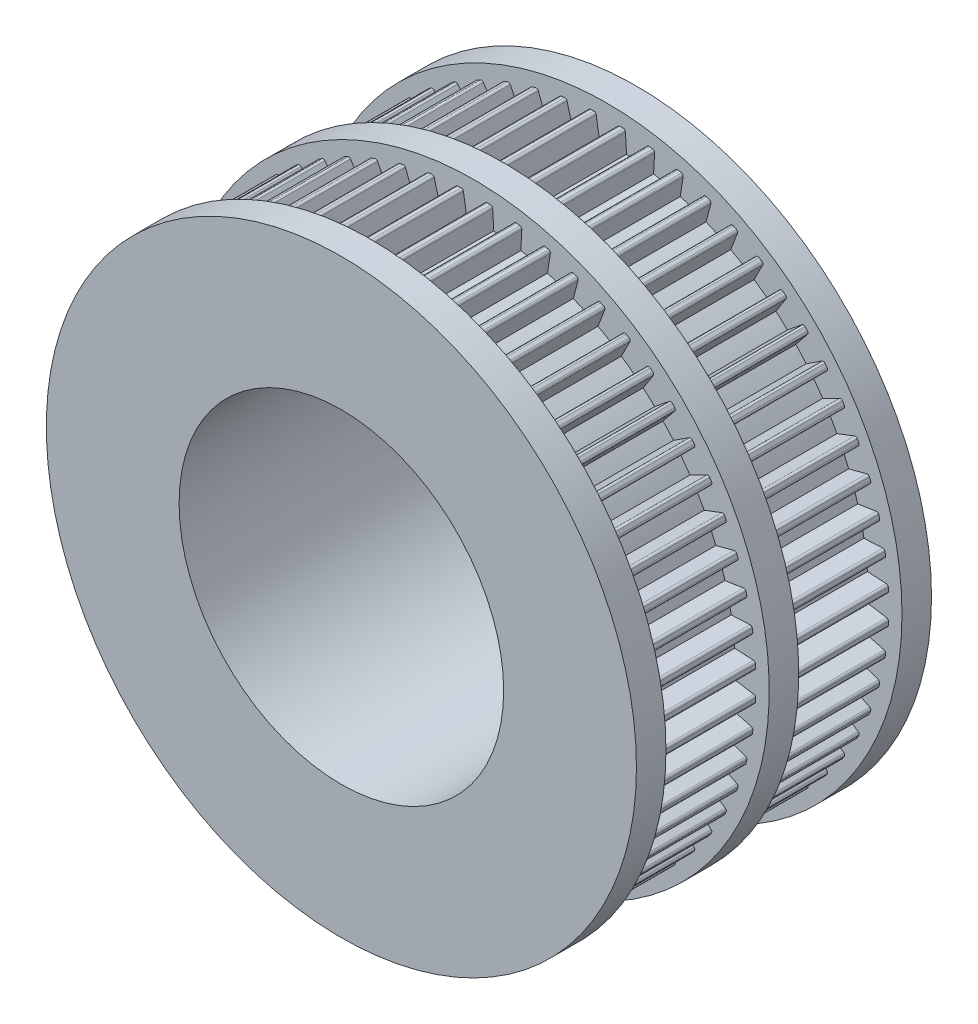
SolidWorks part; units mm, degrees
ref_plane "Front Plane" through (0, 0, 0) normal (0, 0, 1) x (1, 0, 0)
ref_plane "Top Plane" through (0, 0, 0) normal (0, 1, 0) x (1, 0, 0)
ref_plane "Right Plane" through (0, 0, 0) normal (1, 0, 0) x (0, 0, -1)
sketch "Sketch1" plane through (0, 0, 0) normal (0, 0, 1) x (1, 0, 0)
  line L0 (0, 0) -> (0, 9.7797) construction
  line L1 (0, 0) -> (0.9553, 9.0894) construction
  line L2 (-0.7503, 19.0926) -> (-0.527, 17.6995)
  line L3 (1.2496, 19.0664) -> (1.3259, 17.6576) construction
  line L4 (0.7503, 19.0926) -> (0.527, 17.6995)
  line L5 (2.7419, 18.9096) -> (2.3743, 17.5474) construction
  line L6 (1.2496, 19.0664) -> (1.3259, 17.6576)
  line L7 (2.7419, 18.9096) -> (2.3743, 17.5474)
  line L8 (3.2357, 18.8314) -> (3.1644, 17.4223)
  line L9 (4.7034, 18.5194) -> (4.1955, 17.2031)
  line L10 (5.1864, 18.39) -> (4.9682, 16.9961)
  line L11 (6.6135, 17.9263) -> (5.9707, 16.6703)
  line L12 (7.0803, 17.7471) -> (6.7175, 16.3836)
  line L13 (8.451, 17.1368) -> (7.6805, 15.9549)
  line L14 (8.8966, 16.9098) -> (8.3933, 15.5917)
  line L15 (10.196, 16.1595) -> (9.3062, 15.0647)
  line L16 (10.6154, 15.8872) -> (9.9771, 14.629)
  line L17 (11.8293, 15.0052) -> (10.8299, 14.0094)
  line L18 (12.2179, 14.6906) -> (11.4516, 13.5059)
  line L19 (13.333, 13.6865) -> (12.2349, 12.8006)
  line L20 (13.6865, 13.333) -> (12.8006, 12.2349)
  line L21 (14.6906, 12.2179) -> (13.5059, 11.4516)
  line L22 (15.0052, 11.8293) -> (14.0094, 10.8299)
  line L23 (15.8872, 10.6154) -> (14.629, 9.9771)
  line L24 (16.1595, 10.196) -> (15.0647, 9.3062)
  line L25 (16.9098, 8.8966) -> (15.5917, 8.3933)
  line L26 (17.1368, 8.451) -> (15.9549, 7.6805)
  line L27 (17.7471, 7.0803) -> (16.3836, 6.7175)
  line L28 (17.9263, 6.6135) -> (16.6703, 5.9707)
  line L29 (18.39, 5.1864) -> (16.9961, 4.9682)
  line L30 (18.5194, 4.7034) -> (17.2031, 4.1955)
  line L31 (18.8314, 3.2357) -> (17.4223, 3.1644)
  line L32 (18.9096, 2.7419) -> (17.5474, 2.3743)
  line L33 (19.0664, 1.2496) -> (17.6576, 1.3259)
  line L34 (19.0926, 0.7503) -> (17.6995, 0.527)
  line L35 (19.0926, -0.7503) -> (17.6995, -0.527)
  line L36 (19.0664, -1.2496) -> (17.6576, -1.3259)
  line L37 (18.9096, -2.7419) -> (17.5474, -2.3743)
  line L38 (18.8314, -3.2357) -> (17.4223, -3.1644)
  line L39 (18.5194, -4.7034) -> (17.2031, -4.1955)
  line L40 (18.39, -5.1864) -> (16.9961, -4.9682)
  line L41 (17.9263, -6.6135) -> (16.6703, -5.9707)
  line L42 (17.7471, -7.0803) -> (16.3836, -6.7175)
  line L43 (17.1368, -8.451) -> (15.9549, -7.6805)
  line L44 (16.9098, -8.8966) -> (15.5917, -8.3933)
  line L45 (16.1595, -10.196) -> (15.0647, -9.3062)
  line L46 (15.8872, -10.6154) -> (14.629, -9.9771)
  line L47 (15.0052, -11.8293) -> (14.0094, -10.8299)
  line L48 (14.6906, -12.2179) -> (13.5059, -11.4516)
  line L49 (13.6865, -13.333) -> (12.8006, -12.2349)
  line L50 (13.333, -13.6865) -> (12.2349, -12.8006)
  line L51 (12.2179, -14.6906) -> (11.4516, -13.5059)
  line L52 (11.8293, -15.0052) -> (10.8299, -14.0094)
  line L53 (10.6154, -15.8872) -> (9.9771, -14.629)
  line L54 (10.196, -16.1595) -> (9.3062, -15.0647)
  line L55 (8.8966, -16.9098) -> (8.3933, -15.5917)
  line L56 (8.451, -17.1368) -> (7.6805, -15.9549)
  line L57 (7.0803, -17.7471) -> (6.7175, -16.3836)
  line L58 (6.6135, -17.9263) -> (5.9707, -16.6703)
  line L59 (5.1864, -18.39) -> (4.9682, -16.9961)
  line L60 (4.7034, -18.5194) -> (4.1955, -17.2031)
  line L61 (3.2357, -18.8314) -> (3.1644, -17.4223)
  line L62 (2.7419, -18.9096) -> (2.3743, -17.5474)
  line L63 (1.2496, -19.0664) -> (1.3259, -17.6576)
  line L64 (0.7503, -19.0926) -> (0.527, -17.6995)
  line L65 (-0.7503, -19.0926) -> (-0.527, -17.6995)
  line L66 (-1.2496, -19.0664) -> (-1.3259, -17.6576)
  line L67 (-2.7419, -18.9096) -> (-2.3743, -17.5474)
  line L68 (-3.2357, -18.8314) -> (-3.1644, -17.4223)
  line L69 (-4.7034, -18.5194) -> (-4.1955, -17.2031)
  line L70 (-5.1864, -18.39) -> (-4.9682, -16.9961)
  line L71 (-6.6135, -17.9263) -> (-5.9707, -16.6703)
  line L72 (-7.0803, -17.7471) -> (-6.7175, -16.3836)
  line L73 (-8.451, -17.1368) -> (-7.6805, -15.9549)
  line L74 (-8.8966, -16.9098) -> (-8.3933, -15.5917)
  line L75 (-10.196, -16.1595) -> (-9.3062, -15.0647)
  line L76 (-10.6154, -15.8872) -> (-9.9771, -14.629)
  line L77 (-11.8293, -15.0052) -> (-10.8299, -14.0094)
  line L78 (-12.2179, -14.6906) -> (-11.4516, -13.5059)
  line L79 (-13.333, -13.6865) -> (-12.2349, -12.8006)
  line L80 (-13.6865, -13.333) -> (-12.8006, -12.2349)
  line L81 (-14.6906, -12.2179) -> (-13.5059, -11.4516)
  line L82 (-15.0052, -11.8293) -> (-14.0094, -10.8299)
  line L83 (-15.8872, -10.6154) -> (-14.629, -9.9771)
  line L84 (-16.1595, -10.196) -> (-15.0647, -9.3062)
  line L85 (-16.9098, -8.8966) -> (-15.5917, -8.3933)
  line L86 (-17.1368, -8.451) -> (-15.9549, -7.6805)
  line L87 (-17.7471, -7.0803) -> (-16.3836, -6.7175)
  line L88 (-17.9263, -6.6135) -> (-16.6703, -5.9707)
  line L89 (-18.39, -5.1864) -> (-16.9961, -4.9682)
  line L90 (-18.5194, -4.7034) -> (-17.2031, -4.1955)
  line L91 (-18.8314, -3.2357) -> (-17.4223, -3.1644)
  line L92 (-18.9096, -2.7419) -> (-17.5474, -2.3743)
  line L93 (-19.0664, -1.2496) -> (-17.6576, -1.3259)
  line L94 (-19.0926, -0.7503) -> (-17.6995, -0.527)
  line L95 (-19.0926, 0.7503) -> (-17.6995, 0.527)
  line L96 (-19.0664, 1.2496) -> (-17.6576, 1.3259)
  line L97 (-18.9096, 2.7419) -> (-17.5474, 2.3743)
  line L98 (-18.8314, 3.2357) -> (-17.4223, 3.1644)
  line L99 (-18.5194, 4.7034) -> (-17.2031, 4.1955)
  line L100 (-18.39, 5.1864) -> (-16.9961, 4.9682)
  line L101 (-17.9263, 6.6135) -> (-16.6703, 5.9707)
  line L102 (-17.7471, 7.0803) -> (-16.3836, 6.7175)
  line L103 (-17.1368, 8.451) -> (-15.9549, 7.6805)
  line L104 (-16.9098, 8.8966) -> (-15.5917, 8.3933)
  line L105 (-16.1595, 10.196) -> (-15.0647, 9.3062)
  line L106 (-15.8872, 10.6154) -> (-14.629, 9.9771)
  line L107 (-15.0052, 11.8293) -> (-14.0094, 10.8299)
  line L108 (-14.6906, 12.2179) -> (-13.5059, 11.4516)
  line L109 (-13.6865, 13.333) -> (-12.8006, 12.2349)
  line L110 (-13.333, 13.6865) -> (-12.2349, 12.8006)
  line L111 (-12.2179, 14.6906) -> (-11.4516, 13.5059)
  line L112 (-11.8293, 15.0052) -> (-10.8299, 14.0094)
  line L113 (-10.6154, 15.8872) -> (-9.9771, 14.629)
  line L114 (-10.196, 16.1595) -> (-9.3062, 15.0647)
  line L115 (-8.8966, 16.9098) -> (-8.3933, 15.5917)
  line L116 (-8.451, 17.1368) -> (-7.6805, 15.9549)
  line L117 (-7.0803, 17.7471) -> (-6.7175, 16.3836)
  line L118 (-6.6135, 17.9263) -> (-5.9707, 16.6703)
  line L119 (-5.1864, 18.39) -> (-4.9682, 16.9961)
  line L120 (-4.7034, 18.5194) -> (-4.1955, 17.2031)
  line L121 (-3.2357, 18.8314) -> (-3.1644, 17.4223)
  line L122 (-2.7419, 18.9096) -> (-2.3743, 17.5474)
  line L123 (-1.2496, 19.0664) -> (-1.3259, 17.6576)
  arc A0 (2.3743, 17.5474) -> (1.3259, 17.6576) centre (0, 0) ccw construction
  arc A1 (2.7419, 18.9096) -> (1.2496, 19.0664) centre (0, 0) ccw construction
  arc A2 (0.527, 17.6995) -> (-0.527, 17.6995) centre (0, 0) ccw
  arc A3 (0.7503, 19.0926) -> (-0.7503, 19.0926) centre (0, 0) ccw
  arc A4 (2.7419, 18.9096) -> (1.2496, 19.0664) centre (0, 0) ccw
  arc A5 (2.3743, 17.5474) -> (1.3259, 17.6576) centre (0, 0) ccw
  arc A6 (4.7034, 18.5194) -> (3.2357, 18.8314) centre (0, 0) ccw
  arc A7 (4.1955, 17.2031) -> (3.1644, 17.4223) centre (0, 0) ccw
  arc A8 (6.6135, 17.9263) -> (5.1864, 18.39) centre (0, 0) ccw
  arc A9 (5.9707, 16.6703) -> (4.9682, 16.9961) centre (0, 0) ccw
  arc A10 (8.451, 17.1368) -> (7.0803, 17.7471) centre (0, 0) ccw
  arc A11 (7.6805, 15.9549) -> (6.7175, 16.3836) centre (0, 0) ccw
  arc A12 (10.196, 16.1595) -> (8.8966, 16.9098) centre (0, 0) ccw
  arc A13 (9.3062, 15.0647) -> (8.3933, 15.5917) centre (0, 0) ccw
  arc A14 (11.8293, 15.0052) -> (10.6154, 15.8872) centre (0, 0) ccw
  arc A15 (10.8299, 14.0094) -> (9.9771, 14.629) centre (0, 0) ccw
  arc A16 (13.333, 13.6865) -> (12.2179, 14.6906) centre (0, 0) ccw
  arc A17 (12.2349, 12.8006) -> (11.4516, 13.5059) centre (0, 0) ccw
  arc A18 (14.6906, 12.2179) -> (13.6865, 13.333) centre (0, 0) ccw
  arc A19 (13.5059, 11.4516) -> (12.8006, 12.2349) centre (0, 0) ccw
  arc A20 (15.8872, 10.6154) -> (15.0052, 11.8293) centre (0, 0) ccw
  arc A21 (14.629, 9.9771) -> (14.0094, 10.8299) centre (0, 0) ccw
  arc A22 (16.9098, 8.8966) -> (16.1595, 10.196) centre (0, 0) ccw
  arc A23 (15.5917, 8.3933) -> (15.0647, 9.3062) centre (0, 0) ccw
  arc A24 (17.7471, 7.0803) -> (17.1368, 8.451) centre (0, 0) ccw
  arc A25 (16.3836, 6.7175) -> (15.9549, 7.6805) centre (0, 0) ccw
  arc A26 (18.39, 5.1864) -> (17.9263, 6.6135) centre (0, 0) ccw
  arc A27 (16.9961, 4.9682) -> (16.6703, 5.9707) centre (0, 0) ccw
  arc A28 (18.8314, 3.2357) -> (18.5194, 4.7034) centre (0, 0) ccw
  arc A29 (17.4223, 3.1644) -> (17.2031, 4.1955) centre (0, 0) ccw
  arc A30 (19.0664, 1.2496) -> (18.9096, 2.7419) centre (0, 0) ccw
  arc A31 (17.6576, 1.3259) -> (17.5474, 2.3743) centre (0, 0) ccw
  arc A32 (19.0926, -0.7503) -> (19.0926, 0.7503) centre (0, 0) ccw
  arc A33 (17.6995, -0.527) -> (17.6995, 0.527) centre (0, 0) ccw
  arc A34 (18.9096, -2.7419) -> (19.0664, -1.2496) centre (0, 0) ccw
  arc A35 (17.5474, -2.3743) -> (17.6576, -1.3259) centre (0, 0) ccw
  arc A36 (18.5194, -4.7034) -> (18.8314, -3.2357) centre (0, 0) ccw
  arc A37 (17.2031, -4.1955) -> (17.4223, -3.1644) centre (0, 0) ccw
  arc A38 (17.9263, -6.6135) -> (18.39, -5.1864) centre (0, 0) ccw
  arc A39 (16.6703, -5.9707) -> (16.9961, -4.9682) centre (0, 0) ccw
  arc A40 (17.1368, -8.451) -> (17.7471, -7.0803) centre (0, 0) ccw
  arc A41 (15.9549, -7.6805) -> (16.3836, -6.7175) centre (0, 0) ccw
  arc A42 (16.1595, -10.196) -> (16.9098, -8.8966) centre (0, 0) ccw
  arc A43 (15.0647, -9.3062) -> (15.5917, -8.3933) centre (0, 0) ccw
  arc A44 (15.0052, -11.8293) -> (15.8872, -10.6154) centre (0, 0) ccw
  arc A45 (14.0094, -10.8299) -> (14.629, -9.9771) centre (0, 0) ccw
  arc A46 (13.6865, -13.333) -> (14.6906, -12.2179) centre (0, 0) ccw
  arc A47 (12.8006, -12.2349) -> (13.5059, -11.4516) centre (0, 0) ccw
  arc A48 (12.2179, -14.6906) -> (13.333, -13.6865) centre (0, 0) ccw
  arc A49 (11.4516, -13.5059) -> (12.2349, -12.8006) centre (0, 0) ccw
  arc A50 (10.6154, -15.8872) -> (11.8293, -15.0052) centre (0, 0) ccw
  arc A51 (9.9771, -14.629) -> (10.8299, -14.0094) centre (0, 0) ccw
  arc A52 (8.8966, -16.9098) -> (10.196, -16.1595) centre (0, 0) ccw
  arc A53 (8.3933, -15.5917) -> (9.3062, -15.0647) centre (0, 0) ccw
  arc A54 (7.0803, -17.7471) -> (8.451, -17.1368) centre (0, 0) ccw
  arc A55 (6.7175, -16.3836) -> (7.6805, -15.9549) centre (0, 0) ccw
  arc A56 (5.1864, -18.39) -> (6.6135, -17.9263) centre (0, 0) ccw
  arc A57 (4.9682, -16.9961) -> (5.9707, -16.6703) centre (0, 0) ccw
  arc A58 (3.2357, -18.8314) -> (4.7034, -18.5194) centre (0, 0) ccw
  arc A59 (3.1644, -17.4223) -> (4.1955, -17.2031) centre (0, 0) ccw
  arc A60 (1.2496, -19.0664) -> (2.7419, -18.9096) centre (0, 0) ccw
  arc A61 (1.3259, -17.6576) -> (2.3743, -17.5474) centre (0, 0) ccw
  arc A62 (-0.7503, -19.0926) -> (0.7503, -19.0926) centre (0, 0) ccw
  arc A63 (-0.527, -17.6995) -> (0.527, -17.6995) centre (0, 0) ccw
  arc A64 (-2.7419, -18.9096) -> (-1.2496, -19.0664) centre (0, 0) ccw
  arc A65 (-2.3743, -17.5474) -> (-1.3259, -17.6576) centre (0, 0) ccw
  arc A66 (-4.7034, -18.5194) -> (-3.2357, -18.8314) centre (0, 0) ccw
  arc A67 (-4.1955, -17.2031) -> (-3.1644, -17.4223) centre (0, 0) ccw
  arc A68 (-6.6135, -17.9263) -> (-5.1864, -18.39) centre (0, 0) ccw
  arc A69 (-5.9707, -16.6703) -> (-4.9682, -16.9961) centre (0, 0) ccw
  arc A70 (-8.451, -17.1368) -> (-7.0803, -17.7471) centre (0, 0) ccw
  arc A71 (-7.6805, -15.9549) -> (-6.7175, -16.3836) centre (0, 0) ccw
  arc A72 (-10.196, -16.1595) -> (-8.8966, -16.9098) centre (0, 0) ccw
  arc A73 (-9.3062, -15.0647) -> (-8.3933, -15.5917) centre (0, 0) ccw
  arc A74 (-11.8293, -15.0052) -> (-10.6154, -15.8872) centre (0, 0) ccw
  arc A75 (-10.8299, -14.0094) -> (-9.9771, -14.629) centre (0, 0) ccw
  arc A76 (-13.333, -13.6865) -> (-12.2179, -14.6906) centre (0, 0) ccw
  arc A77 (-12.2349, -12.8006) -> (-11.4516, -13.5059) centre (0, 0) ccw
  arc A78 (-14.6906, -12.2179) -> (-13.6865, -13.333) centre (0, 0) ccw
  arc A79 (-13.5059, -11.4516) -> (-12.8006, -12.2349) centre (0, 0) ccw
  arc A80 (-15.8872, -10.6154) -> (-15.0052, -11.8293) centre (0, 0) ccw
  arc A81 (-14.629, -9.9771) -> (-14.0094, -10.8299) centre (0, 0) ccw
  arc A82 (-16.9098, -8.8966) -> (-16.1595, -10.196) centre (0, 0) ccw
  arc A83 (-15.5917, -8.3933) -> (-15.0647, -9.3062) centre (0, 0) ccw
  arc A84 (-17.7471, -7.0803) -> (-17.1368, -8.451) centre (0, 0) ccw
  arc A85 (-16.3836, -6.7175) -> (-15.9549, -7.6805) centre (0, 0) ccw
  arc A86 (-18.39, -5.1864) -> (-17.9263, -6.6135) centre (0, 0) ccw
  arc A87 (-16.9961, -4.9682) -> (-16.6703, -5.9707) centre (0, 0) ccw
  arc A88 (-18.8314, -3.2357) -> (-18.5194, -4.7034) centre (0, 0) ccw
  arc A89 (-17.4223, -3.1644) -> (-17.2031, -4.1955) centre (0, 0) ccw
  arc A90 (-19.0664, -1.2496) -> (-18.9096, -2.7419) centre (0, 0) ccw
  arc A91 (-17.6576, -1.3259) -> (-17.5474, -2.3743) centre (0, 0) ccw
  arc A92 (-19.0926, 0.7503) -> (-19.0926, -0.7503) centre (0, 0) ccw
  arc A93 (-17.6995, 0.527) -> (-17.6995, -0.527) centre (0, 0) ccw
  arc A94 (-18.9096, 2.7419) -> (-19.0664, 1.2496) centre (0, 0) ccw
  arc A95 (-17.5474, 2.3743) -> (-17.6576, 1.3259) centre (0, 0) ccw
  arc A96 (-18.5194, 4.7034) -> (-18.8314, 3.2357) centre (0, 0) ccw
  arc A97 (-17.2031, 4.1955) -> (-17.4223, 3.1644) centre (0, 0) ccw
  arc A98 (-17.9263, 6.6135) -> (-18.39, 5.1864) centre (0, 0) ccw
  arc A99 (-16.6703, 5.9707) -> (-16.9961, 4.9682) centre (0, 0) ccw
  arc A100 (-17.1368, 8.451) -> (-17.7471, 7.0803) centre (0, 0) ccw
  arc A101 (-15.9549, 7.6805) -> (-16.3836, 6.7175) centre (0, 0) ccw
  arc A102 (-16.1595, 10.196) -> (-16.9098, 8.8966) centre (0, 0) ccw
  arc A103 (-15.0647, 9.3062) -> (-15.5917, 8.3933) centre (0, 0) ccw
  arc A104 (-15.0052, 11.8293) -> (-15.8872, 10.6154) centre (0, 0) ccw
  arc A105 (-14.0094, 10.8299) -> (-14.629, 9.9771) centre (0, 0) ccw
  arc A106 (-13.6865, 13.333) -> (-14.6906, 12.2179) centre (0, 0) ccw
  arc A107 (-12.8006, 12.2349) -> (-13.5059, 11.4516) centre (0, 0) ccw
  arc A108 (-12.2179, 14.6906) -> (-13.333, 13.6865) centre (0, 0) ccw
  arc A109 (-11.4516, 13.5059) -> (-12.2349, 12.8006) centre (0, 0) ccw
  arc A110 (-10.6154, 15.8872) -> (-11.8293, 15.0052) centre (0, 0) ccw
  arc A111 (-9.9771, 14.629) -> (-10.8299, 14.0094) centre (0, 0) ccw
  arc A112 (-8.8966, 16.9098) -> (-10.196, 16.1595) centre (0, 0) ccw
  arc A113 (-8.3933, 15.5917) -> (-9.3062, 15.0647) centre (0, 0) ccw
  arc A114 (-7.0803, 17.7471) -> (-8.451, 17.1368) centre (0, 0) ccw
  arc A115 (-6.7175, 16.3836) -> (-7.6805, 15.9549) centre (0, 0) ccw
  arc A116 (-5.1864, 18.39) -> (-6.6135, 17.9263) centre (0, 0) ccw
  arc A117 (-4.9682, 16.9961) -> (-5.9707, 16.6703) centre (0, 0) ccw
  arc A118 (-3.2357, 18.8314) -> (-4.7034, 18.5194) centre (0, 0) ccw
  arc A119 (-3.1644, 17.4223) -> (-4.1955, 17.2031) centre (0, 0) ccw
  arc A120 (-1.2496, 19.0664) -> (-2.7419, 18.9096) centre (0, 0) ccw
  arc A121 (-1.3259, 17.6576) -> (-2.3743, 17.5474) centre (0, 0) ccw
  point P1 (0, 19.1073)
  point P2 (1.9973, 19.0027)
  point P253 (0, 0)
  dimension "D1" = 1.4
  dimension "D2" = 0.8
  dimension "D3" = 0.5
  dimension "D4" = 2
  dimension "D5" = 60
sketch "Sketch2" plane through (0, 0, 0) normal (0, 0, 1) x (1, 0, 0)
  circle A0 centre (0, 0) radius 19.1073
extrude "Boss-Extrude1" add sketch "Sketch2" along normal blind 7
extrude "Cut-Extrude1" cut sketch "Sketch1" along normal blind 22
fillet "Fillet1" radius 0.15 4 edges at (-8.3933, 15.5917, 3.5) (-8.8966, 16.9098, 3.5) (-7.6805, 15.9549, 3.5) (-8.451, 17.1368, 3.5)
sketch "Sketch3" plane through (0, 0, 0) normal (0, 0, -1) x (-1, 0, 0)
  circle A0 centre (0, 0) radius 8
  dimension "D1" = 16
extrude "Cut-Extrude2" cut sketch "Sketch3" against normal blind 22
sketch "Sketch5" plane through (0, 0, 7) normal (0, 0, 1) x (1, 0, 0)
  line L0 (-0.527, 17.6995) -> (-0.7503, 19.0926) construction
  line L1 (-1.2496, 19.0664) -> (-1.3259, 17.6576) construction
  line L2 (0.7503, 19.0926) -> (0.7291, 18.9607)
  line L3 (1.2568, 18.9331) -> (1.2496, 19.0664)
  line L4 (-0.7291, 18.9607) -> (-0.7503, 19.0926)
  line L5 (-1.2496, 19.0664) -> (-1.2568, 18.9331)
  line L6 (2.7419, 18.9096) -> (2.7071, 18.7807)
  line L7 (3.229, 18.698) -> (3.2357, 18.8314)
  line L8 (4.7034, 18.5194) -> (4.6554, 18.3948)
  line L9 (5.1657, 18.2581) -> (5.1864, 18.39)
  line L10 (6.6135, 17.9263) -> (6.5526, 17.8074)
  line L11 (7.0459, 17.6181) -> (7.0803, 17.7471)
  line L12 (8.451, 17.1368) -> (8.3781, 17.0249)
  line L13 (8.8489, 16.7851) -> (8.8966, 16.9098)
  line L14 (10.196, 16.1595) -> (10.1118, 16.0559)
  line L15 (10.555, 15.7681) -> (10.6154, 15.8872)
  line L16 (11.8293, 15.0052) -> (11.7347, 14.911)
  line L17 (12.1454, 14.5785) -> (12.2179, 14.6906)
  line L18 (13.333, 13.6865) -> (13.2291, 13.6027)
  line L19 (13.6027, 13.2291) -> (13.6865, 13.333)
  line L20 (14.6906, 12.2179) -> (14.5785, 12.1454)
  line L21 (14.911, 11.7347) -> (15.0052, 11.8293)
  line L22 (15.8872, 10.6154) -> (15.7681, 10.555)
  line L23 (16.0559, 10.1118) -> (16.1595, 10.196)
  line L24 (16.9098, 8.8966) -> (16.7851, 8.8489)
  line L25 (17.0249, 8.3781) -> (17.1368, 8.451)
  line L26 (17.7471, 7.0803) -> (17.6181, 7.0459)
  line L27 (17.8074, 6.5526) -> (17.9263, 6.6135)
  line L28 (18.39, 5.1864) -> (18.2581, 5.1657)
  line L29 (18.3948, 4.6554) -> (18.5194, 4.7034)
  line L30 (18.8314, 3.2357) -> (18.698, 3.229)
  line L31 (18.7807, 2.7071) -> (18.9096, 2.7419)
  line L32 (19.0664, 1.2496) -> (18.9331, 1.2568)
  line L33 (18.9607, 0.7291) -> (19.0926, 0.7503)
  line L34 (19.0926, -0.7503) -> (18.9607, -0.7291)
  line L35 (18.9331, -1.2568) -> (19.0664, -1.2496)
  line L36 (18.9096, -2.7419) -> (18.7807, -2.7071)
  line L37 (18.698, -3.229) -> (18.8314, -3.2357)
  line L38 (18.5194, -4.7034) -> (18.3948, -4.6554)
  line L39 (18.2581, -5.1657) -> (18.39, -5.1864)
  line L40 (17.9263, -6.6135) -> (17.8074, -6.5526)
  line L41 (17.6181, -7.0459) -> (17.7471, -7.0803)
  line L42 (17.1368, -8.451) -> (17.0249, -8.3781)
  line L43 (16.7851, -8.8489) -> (16.9098, -8.8966)
  line L44 (16.1595, -10.196) -> (16.0559, -10.1118)
  line L45 (15.7681, -10.555) -> (15.8872, -10.6154)
  line L46 (15.0052, -11.8293) -> (14.911, -11.7347)
  line L47 (14.5785, -12.1454) -> (14.6906, -12.2179)
  line L48 (13.6865, -13.333) -> (13.6027, -13.2291)
  line L49 (13.2291, -13.6027) -> (13.333, -13.6865)
  line L50 (12.2179, -14.6906) -> (12.1454, -14.5785)
  line L51 (11.7347, -14.911) -> (11.8293, -15.0052)
  line L52 (10.6154, -15.8872) -> (10.555, -15.7681)
  line L53 (10.1118, -16.0559) -> (10.196, -16.1595)
  line L54 (8.8966, -16.9098) -> (8.8489, -16.7851)
  line L55 (8.3781, -17.0249) -> (8.451, -17.1368)
  line L56 (7.0803, -17.7471) -> (7.0459, -17.6181)
  line L57 (6.5526, -17.8074) -> (6.6135, -17.9263)
  line L58 (5.1864, -18.39) -> (5.1657, -18.2581)
  line L59 (4.6554, -18.3948) -> (4.7034, -18.5194)
  line L60 (3.2357, -18.8314) -> (3.229, -18.698)
  line L61 (2.7071, -18.7807) -> (2.7419, -18.9096)
  line L62 (1.2496, -19.0664) -> (1.2568, -18.9331)
  line L63 (0.7291, -18.9607) -> (0.7503, -19.0926)
  line L64 (-0.7503, -19.0926) -> (-0.7291, -18.9607)
  line L65 (-1.2568, -18.9331) -> (-1.2496, -19.0664)
  line L66 (-2.7419, -18.9096) -> (-2.7071, -18.7807)
  line L67 (-3.229, -18.698) -> (-3.2357, -18.8314)
  line L68 (-4.7034, -18.5194) -> (-4.6554, -18.3948)
  line L69 (-5.1657, -18.2581) -> (-5.1864, -18.39)
  line L70 (-6.6135, -17.9263) -> (-6.5526, -17.8074)
  line L71 (-7.0459, -17.6181) -> (-7.0803, -17.7471)
  line L72 (-8.451, -17.1368) -> (-8.3781, -17.0249)
  line L73 (-8.8489, -16.7851) -> (-8.8966, -16.9098)
  line L74 (-10.196, -16.1595) -> (-10.1118, -16.0559)
  line L75 (-10.555, -15.7681) -> (-10.6154, -15.8872)
  line L76 (-11.8293, -15.0052) -> (-11.7347, -14.911)
  line L77 (-12.1454, -14.5785) -> (-12.2179, -14.6906)
  line L78 (-13.333, -13.6865) -> (-13.2291, -13.6027)
  line L79 (-13.6027, -13.2291) -> (-13.6865, -13.333)
  line L80 (-14.6906, -12.2179) -> (-14.5785, -12.1454)
  line L81 (-14.911, -11.7347) -> (-15.0052, -11.8293)
  line L82 (-15.8872, -10.6154) -> (-15.7681, -10.555)
  line L83 (-16.0559, -10.1118) -> (-16.1595, -10.196)
  line L84 (-16.9098, -8.8966) -> (-16.7851, -8.8489)
  line L85 (-17.0249, -8.3781) -> (-17.1368, -8.451)
  line L86 (-17.7471, -7.0803) -> (-17.6181, -7.0459)
  line L87 (-17.8074, -6.5526) -> (-17.9263, -6.6135)
  line L88 (-18.39, -5.1864) -> (-18.2581, -5.1657)
  line L89 (-18.3948, -4.6554) -> (-18.5194, -4.7034)
  line L90 (-18.8314, -3.2357) -> (-18.698, -3.229)
  line L91 (-18.7807, -2.7071) -> (-18.9096, -2.7419)
  line L92 (-19.0664, -1.2496) -> (-18.9331, -1.2568)
  line L93 (-18.9607, -0.7291) -> (-19.0926, -0.7503)
  line L94 (-19.0926, 0.7503) -> (-18.9607, 0.7291)
  line L95 (-18.9331, 1.2568) -> (-19.0664, 1.2496)
  line L96 (-18.9096, 2.7419) -> (-18.7807, 2.7071)
  line L97 (-18.698, 3.229) -> (-18.8314, 3.2357)
  line L98 (-18.5194, 4.7034) -> (-18.3948, 4.6554)
  line L99 (-18.2581, 5.1657) -> (-18.39, 5.1864)
  line L100 (-17.9263, 6.6135) -> (-17.8074, 6.5526)
  line L101 (-17.6181, 7.0459) -> (-17.7471, 7.0803)
  line L102 (-17.1368, 8.451) -> (-17.0249, 8.3781)
  line L103 (-16.7851, 8.8489) -> (-16.9098, 8.8966)
  line L104 (-16.1595, 10.196) -> (-16.0559, 10.1118)
  line L105 (-15.7681, 10.555) -> (-15.8872, 10.6154)
  line L106 (-15.0052, 11.8293) -> (-14.911, 11.7347)
  line L107 (-14.5785, 12.1454) -> (-14.6906, 12.2179)
  line L108 (-13.6865, 13.333) -> (-13.6027, 13.2291)
  line L109 (-13.2291, 13.6027) -> (-13.333, 13.6865)
  line L110 (-12.2179, 14.6906) -> (-12.1454, 14.5785)
  line L111 (-11.7347, 14.911) -> (-11.8293, 15.0052)
  line L112 (-10.6154, 15.8872) -> (-10.555, 15.7681)
  line L113 (-10.1118, 16.0559) -> (-10.196, 16.1595)
  line L114 (-8.8966, 16.9098) -> (-8.8489, 16.7851)
  line L115 (-8.3781, 17.0249) -> (-8.451, 17.1368)
  line L116 (-7.0803, 17.7471) -> (-7.0459, 17.6181)
  line L117 (-6.5526, 17.8074) -> (-6.6135, 17.9263)
  line L118 (-5.1864, 18.39) -> (-5.1657, 18.2581)
  line L119 (-4.6554, 18.3948) -> (-4.7034, 18.5194)
  line L120 (-3.2357, 18.8314) -> (-3.229, 18.698)
  line L121 (-2.7071, 18.7807) -> (-2.7419, 18.9096)
  arc A0 (-0.7503, 19.0926) -> (-1.2496, 19.0664) centre (0, 0) ccw construction
  arc A2 (-0.8842, 19.0869) -> (-0.7291, 18.9607) centre (-0.8772, 18.937) cw
  arc A3 (-1.1158, 19.0747) -> (-1.2568, 18.9331) centre (-1.107, 18.925) ccw
  arc A4 (-0.7503, 19.0926) -> (-0.8842, 19.0869) centre (0, 0) ccw
  arc A5 (-1.1158, 19.0747) -> (-1.2496, 19.0664) centre (0, 0) ccw
  arc A6 (0.8842, 19.0869) -> (0.7291, 18.9607) centre (0.8772, 18.937) ccw
  arc A7 (0.8842, 19.0869) -> (0.7503, 19.0926) centre (0, 0) ccw
  arc A8 (1.1158, 19.0747) -> (1.2568, 18.9331) centre (1.107, 18.925) cw
  arc A9 (1.2496, 19.0664) -> (1.1158, 19.0747) centre (0, 0) ccw
  arc A10 (2.8745, 18.8899) -> (2.7071, 18.7807) centre (2.8519, 18.7416) ccw
  arc A11 (2.8745, 18.8899) -> (2.7419, 18.9096) centre (0, 0) ccw
  arc A12 (3.1035, 18.8536) -> (3.229, 18.698) centre (3.0792, 18.7056) cw
  arc A13 (3.2357, 18.8314) -> (3.1035, 18.8536) centre (0, 0) ccw
  arc A14 (4.8332, 18.4859) -> (4.6554, 18.3948) centre (4.7953, 18.3408) ccw
  arc A15 (4.8332, 18.4859) -> (4.7034, 18.5194) centre (0, 0) ccw
  arc A16 (5.0573, 18.4259) -> (5.1657, 18.2581) centre (5.0176, 18.2813) cw
  arc A17 (5.1864, 18.39) -> (5.0573, 18.4259) centre (0, 0) ccw
  arc A18 (6.7391, 17.8794) -> (6.5526, 17.8074) centre (6.6862, 17.7391) ccw
  arc A19 (6.7391, 17.8794) -> (6.6135, 17.9263) centre (0, 0) ccw
  arc A20 (6.9556, 17.7963) -> (7.0459, 17.6181) centre (6.901, 17.6566) cw
  arc A21 (7.0803, 17.7471) -> (6.9556, 17.7963) centre (0, 0) ccw
  arc A22 (8.5711, 17.0771) -> (8.3781, 17.0249) centre (8.5038, 16.943) ccw
  arc A23 (8.5711, 17.0771) -> (8.451, 17.1368) centre (0, 0) ccw
  arc A24 (8.7777, 16.9718) -> (8.8489, 16.7851) centre (8.7088, 16.8386) cw
  arc A25 (8.8966, 16.9098) -> (8.7777, 16.9718) centre (0, 0) ccw
  arc A26 (10.3092, 16.0876) -> (10.1118, 16.0559) centre (10.2282, 15.9613) ccw
  arc A27 (10.3092, 16.0876) -> (10.196, 16.1595) centre (0, 0) ccw
  arc A28 (10.5037, 15.9613) -> (10.555, 15.7681) centre (10.4212, 15.836) cw
  arc A29 (10.6154, 15.8872) -> (10.5037, 15.9613) centre (0, 0) ccw
  arc A30 (11.9343, 14.9219) -> (11.7347, 14.911) centre (11.8406, 14.8047) ccw
  arc A31 (11.9343, 14.9219) -> (11.8293, 15.0052) centre (0, 0) ccw
  arc A32 (12.1145, 14.7759) -> (12.1454, 14.5785) centre (12.0194, 14.6599) cw
  arc A33 (12.2179, 14.6906) -> (12.1145, 14.7759) centre (0, 0) ccw
  arc A34 (13.4287, 13.5927) -> (13.2291, 13.6027) centre (13.3233, 13.486) ccw
  arc A35 (13.4287, 13.5927) -> (13.333, 13.6865) centre (0, 0) ccw
  arc A36 (13.5927, 13.4287) -> (13.6027, 13.2291) centre (13.486, 13.3233) cw
  arc A37 (13.6865, 13.333) -> (13.5927, 13.4287) centre (0, 0) ccw
  arc A38 (14.7759, 12.1145) -> (14.5785, 12.1454) centre (14.6599, 12.0194) ccw
  arc A39 (14.7759, 12.1145) -> (14.6906, 12.2179) centre (0, 0) ccw
  arc A40 (14.9219, 11.9343) -> (14.911, 11.7347) centre (14.8047, 11.8406) cw
  arc A41 (15.0052, 11.8293) -> (14.9219, 11.9343) centre (0, 0) ccw
  arc A42 (15.9613, 10.5037) -> (15.7681, 10.555) centre (15.836, 10.4212) ccw
  arc A43 (15.9613, 10.5037) -> (15.8872, 10.6154) centre (0, 0) ccw
  arc A44 (16.0876, 10.3092) -> (16.0559, 10.1118) centre (15.9613, 10.2282) cw
  arc A45 (16.1595, 10.196) -> (16.0876, 10.3092) centre (0, 0) ccw
  arc A46 (16.9718, 8.7777) -> (16.7851, 8.8489) centre (16.8386, 8.7088) ccw
  arc A47 (16.9718, 8.7777) -> (16.9098, 8.8966) centre (0, 0) ccw
  arc A48 (17.0771, 8.5711) -> (17.0249, 8.3781) centre (16.943, 8.5038) cw
  arc A49 (17.1368, 8.451) -> (17.0771, 8.5711) centre (0, 0) ccw
  arc A50 (17.7963, 6.9556) -> (17.6181, 7.0459) centre (17.6566, 6.901) ccw
  arc A51 (17.7963, 6.9556) -> (17.7471, 7.0803) centre (0, 0) ccw
  arc A52 (17.8794, 6.7391) -> (17.8074, 6.5526) centre (17.7391, 6.6862) cw
  arc A53 (17.9263, 6.6135) -> (17.8794, 6.7391) centre (0, 0) ccw
  arc A54 (18.4259, 5.0573) -> (18.2581, 5.1657) centre (18.2813, 5.0176) ccw
  arc A55 (18.4259, 5.0573) -> (18.39, 5.1864) centre (0, 0) ccw
  arc A56 (18.4859, 4.8332) -> (18.3948, 4.6554) centre (18.3408, 4.7953) cw
  arc A57 (18.5194, 4.7034) -> (18.4859, 4.8332) centre (0, 0) ccw
  arc A58 (18.8536, 3.1035) -> (18.698, 3.229) centre (18.7056, 3.0792) ccw
  arc A59 (18.8536, 3.1035) -> (18.8314, 3.2357) centre (0, 0) ccw
  arc A60 (18.8899, 2.8745) -> (18.7807, 2.7071) centre (18.7416, 2.8519) cw
  arc A61 (18.9096, 2.7419) -> (18.8899, 2.8745) centre (0, 0) ccw
  arc A62 (19.0747, 1.1158) -> (18.9331, 1.2568) centre (18.925, 1.107) ccw
  arc A63 (19.0747, 1.1158) -> (19.0664, 1.2496) centre (0, 0) ccw
  arc A64 (19.0869, 0.8842) -> (18.9607, 0.7291) centre (18.937, 0.8772) cw
  arc A65 (19.0926, 0.7503) -> (19.0869, 0.8842) centre (0, 0) ccw
  arc A66 (19.0869, -0.8842) -> (18.9607, -0.7291) centre (18.937, -0.8772) ccw
  arc A67 (19.0869, -0.8842) -> (19.0926, -0.7503) centre (0, 0) ccw
  arc A68 (19.0747, -1.1158) -> (18.9331, -1.2568) centre (18.925, -1.107) cw
  arc A69 (19.0664, -1.2496) -> (19.0747, -1.1158) centre (0, 0) ccw
  arc A70 (18.8899, -2.8745) -> (18.7807, -2.7071) centre (18.7416, -2.8519) ccw
  arc A71 (18.8899, -2.8745) -> (18.9096, -2.7419) centre (0, 0) ccw
  arc A72 (18.8536, -3.1035) -> (18.698, -3.229) centre (18.7056, -3.0792) cw
  arc A73 (18.8314, -3.2357) -> (18.8536, -3.1035) centre (0, 0) ccw
  arc A74 (18.4859, -4.8332) -> (18.3948, -4.6554) centre (18.3408, -4.7953) ccw
  arc A75 (18.4859, -4.8332) -> (18.5194, -4.7034) centre (0, 0) ccw
  arc A76 (18.4259, -5.0573) -> (18.2581, -5.1657) centre (18.2813, -5.0176) cw
  arc A77 (18.39, -5.1864) -> (18.4259, -5.0573) centre (0, 0) ccw
  arc A78 (17.8794, -6.7391) -> (17.8074, -6.5526) centre (17.7391, -6.6862) ccw
  arc A79 (17.8794, -6.7391) -> (17.9263, -6.6135) centre (0, 0) ccw
  arc A80 (17.7963, -6.9556) -> (17.6181, -7.0459) centre (17.6566, -6.901) cw
  arc A81 (17.7471, -7.0803) -> (17.7963, -6.9556) centre (0, 0) ccw
  arc A82 (17.0771, -8.5711) -> (17.0249, -8.3781) centre (16.943, -8.5038) ccw
  arc A83 (17.0771, -8.5711) -> (17.1368, -8.451) centre (0, 0) ccw
  arc A84 (16.9718, -8.7777) -> (16.7851, -8.8489) centre (16.8386, -8.7088) cw
  arc A85 (16.9098, -8.8966) -> (16.9718, -8.7777) centre (0, 0) ccw
  arc A86 (16.0876, -10.3092) -> (16.0559, -10.1118) centre (15.9613, -10.2282) ccw
  arc A87 (16.0876, -10.3092) -> (16.1595, -10.196) centre (0, 0) ccw
  arc A88 (15.9613, -10.5037) -> (15.7681, -10.555) centre (15.836, -10.4212) cw
  arc A89 (15.8872, -10.6154) -> (15.9613, -10.5037) centre (0, 0) ccw
  arc A90 (14.9219, -11.9343) -> (14.911, -11.7347) centre (14.8047, -11.8406) ccw
  arc A91 (14.9219, -11.9343) -> (15.0052, -11.8293) centre (0, 0) ccw
  arc A92 (14.7759, -12.1145) -> (14.5785, -12.1454) centre (14.6599, -12.0194) cw
  arc A93 (14.6906, -12.2179) -> (14.7759, -12.1145) centre (0, 0) ccw
  arc A94 (13.5927, -13.4287) -> (13.6027, -13.2291) centre (13.486, -13.3233) ccw
  arc A95 (13.5927, -13.4287) -> (13.6865, -13.333) centre (0, 0) ccw
  arc A96 (13.4287, -13.5927) -> (13.2291, -13.6027) centre (13.3233, -13.486) cw
  arc A97 (13.333, -13.6865) -> (13.4287, -13.5927) centre (0, 0) ccw
  arc A98 (12.1145, -14.7759) -> (12.1454, -14.5785) centre (12.0194, -14.6599) ccw
  arc A99 (12.1145, -14.7759) -> (12.2179, -14.6906) centre (0, 0) ccw
  arc A100 (11.9343, -14.9219) -> (11.7347, -14.911) centre (11.8406, -14.8047) cw
  arc A101 (11.8293, -15.0052) -> (11.9343, -14.9219) centre (0, 0) ccw
  arc A102 (10.5037, -15.9613) -> (10.555, -15.7681) centre (10.4212, -15.836) ccw
  arc A103 (10.5037, -15.9613) -> (10.6154, -15.8872) centre (0, 0) ccw
  arc A104 (10.3092, -16.0876) -> (10.1118, -16.0559) centre (10.2282, -15.9613) cw
  arc A105 (10.196, -16.1595) -> (10.3092, -16.0876) centre (0, 0) ccw
  arc A106 (8.7777, -16.9718) -> (8.8489, -16.7851) centre (8.7088, -16.8386) ccw
  arc A107 (8.7777, -16.9718) -> (8.8966, -16.9098) centre (0, 0) ccw
  arc A108 (8.5711, -17.0771) -> (8.3781, -17.0249) centre (8.5038, -16.943) cw
  arc A109 (8.451, -17.1368) -> (8.5711, -17.0771) centre (0, 0) ccw
  arc A110 (6.9556, -17.7963) -> (7.0459, -17.6181) centre (6.901, -17.6566) ccw
  arc A111 (6.9556, -17.7963) -> (7.0803, -17.7471) centre (0, 0) ccw
  arc A112 (6.7391, -17.8794) -> (6.5526, -17.8074) centre (6.6862, -17.7391) cw
  arc A113 (6.6135, -17.9263) -> (6.7391, -17.8794) centre (0, 0) ccw
  arc A114 (5.0573, -18.4259) -> (5.1657, -18.2581) centre (5.0176, -18.2813) ccw
  arc A115 (5.0573, -18.4259) -> (5.1864, -18.39) centre (0, 0) ccw
  arc A116 (4.8332, -18.4859) -> (4.6554, -18.3948) centre (4.7953, -18.3408) cw
  arc A117 (4.7034, -18.5194) -> (4.8332, -18.4859) centre (0, 0) ccw
  arc A118 (3.1035, -18.8536) -> (3.229, -18.698) centre (3.0792, -18.7056) ccw
  arc A119 (3.1035, -18.8536) -> (3.2357, -18.8314) centre (0, 0) ccw
  arc A120 (2.8745, -18.8899) -> (2.7071, -18.7807) centre (2.8519, -18.7416) cw
  arc A121 (2.7419, -18.9096) -> (2.8745, -18.8899) centre (0, 0) ccw
  arc A122 (1.1158, -19.0747) -> (1.2568, -18.9331) centre (1.107, -18.925) ccw
  arc A123 (1.1158, -19.0747) -> (1.2496, -19.0664) centre (0, 0) ccw
  arc A124 (0.8842, -19.0869) -> (0.7291, -18.9607) centre (0.8772, -18.937) cw
  arc A125 (0.7503, -19.0926) -> (0.8842, -19.0869) centre (0, 0) ccw
  arc A126 (-0.8842, -19.0869) -> (-0.7291, -18.9607) centre (-0.8772, -18.937) ccw
  arc A127 (-0.8842, -19.0869) -> (-0.7503, -19.0926) centre (0, 0) ccw
  arc A128 (-1.1158, -19.0747) -> (-1.2568, -18.9331) centre (-1.107, -18.925) cw
  arc A129 (-1.2496, -19.0664) -> (-1.1158, -19.0747) centre (0, 0) ccw
  arc A130 (-2.8745, -18.8899) -> (-2.7071, -18.7807) centre (-2.8519, -18.7416) ccw
  arc A131 (-2.8745, -18.8899) -> (-2.7419, -18.9096) centre (0, 0) ccw
  arc A132 (-3.1035, -18.8536) -> (-3.229, -18.698) centre (-3.0792, -18.7056) cw
  arc A133 (-3.2357, -18.8314) -> (-3.1035, -18.8536) centre (0, 0) ccw
  arc A134 (-4.8332, -18.4859) -> (-4.6554, -18.3948) centre (-4.7953, -18.3408) ccw
  arc A135 (-4.8332, -18.4859) -> (-4.7034, -18.5194) centre (0, 0) ccw
  arc A136 (-5.0573, -18.4259) -> (-5.1657, -18.2581) centre (-5.0176, -18.2813) cw
  arc A137 (-5.1864, -18.39) -> (-5.0573, -18.4259) centre (0, 0) ccw
  arc A138 (-6.7391, -17.8794) -> (-6.5526, -17.8074) centre (-6.6862, -17.7391) ccw
  arc A139 (-6.7391, -17.8794) -> (-6.6135, -17.9263) centre (0, 0) ccw
  arc A140 (-6.9556, -17.7963) -> (-7.0459, -17.6181) centre (-6.901, -17.6566) cw
  arc A141 (-7.0803, -17.7471) -> (-6.9556, -17.7963) centre (0, 0) ccw
  arc A142 (-8.5711, -17.0771) -> (-8.3781, -17.0249) centre (-8.5038, -16.943) ccw
  arc A143 (-8.5711, -17.0771) -> (-8.451, -17.1368) centre (0, 0) ccw
  arc A144 (-8.7777, -16.9718) -> (-8.8489, -16.7851) centre (-8.7088, -16.8386) cw
  arc A145 (-8.8966, -16.9098) -> (-8.7777, -16.9718) centre (0, 0) ccw
  arc A146 (-10.3092, -16.0876) -> (-10.1118, -16.0559) centre (-10.2282, -15.9613) ccw
  arc A147 (-10.3092, -16.0876) -> (-10.196, -16.1595) centre (0, 0) ccw
  arc A148 (-10.5037, -15.9613) -> (-10.555, -15.7681) centre (-10.4212, -15.836) cw
  arc A149 (-10.6154, -15.8872) -> (-10.5037, -15.9613) centre (0, 0) ccw
  arc A150 (-11.9343, -14.9219) -> (-11.7347, -14.911) centre (-11.8406, -14.8047) ccw
  arc A151 (-11.9343, -14.9219) -> (-11.8293, -15.0052) centre (0, 0) ccw
  arc A152 (-12.1145, -14.7759) -> (-12.1454, -14.5785) centre (-12.0194, -14.6599) cw
  arc A153 (-12.2179, -14.6906) -> (-12.1145, -14.7759) centre (0, 0) ccw
  arc A154 (-13.4287, -13.5927) -> (-13.2291, -13.6027) centre (-13.3233, -13.486) ccw
  arc A155 (-13.4287, -13.5927) -> (-13.333, -13.6865) centre (0, 0) ccw
  arc A156 (-13.5927, -13.4287) -> (-13.6027, -13.2291) centre (-13.486, -13.3233) cw
  arc A157 (-13.6865, -13.333) -> (-13.5927, -13.4287) centre (0, 0) ccw
  arc A158 (-14.7759, -12.1145) -> (-14.5785, -12.1454) centre (-14.6599, -12.0194) ccw
  arc A159 (-14.7759, -12.1145) -> (-14.6906, -12.2179) centre (0, 0) ccw
  arc A160 (-14.9219, -11.9343) -> (-14.911, -11.7347) centre (-14.8047, -11.8406) cw
  arc A161 (-15.0052, -11.8293) -> (-14.9219, -11.9343) centre (0, 0) ccw
  arc A162 (-15.9613, -10.5037) -> (-15.7681, -10.555) centre (-15.836, -10.4212) ccw
  arc A163 (-15.9613, -10.5037) -> (-15.8872, -10.6154) centre (0, 0) ccw
  arc A164 (-16.0876, -10.3092) -> (-16.0559, -10.1118) centre (-15.9613, -10.2282) cw
  arc A165 (-16.1595, -10.196) -> (-16.0876, -10.3092) centre (0, 0) ccw
  arc A166 (-16.9718, -8.7777) -> (-16.7851, -8.8489) centre (-16.8386, -8.7088) ccw
  arc A167 (-16.9718, -8.7777) -> (-16.9098, -8.8966) centre (0, 0) ccw
  arc A168 (-17.0771, -8.5711) -> (-17.0249, -8.3781) centre (-16.943, -8.5038) cw
  arc A169 (-17.1368, -8.451) -> (-17.0771, -8.5711) centre (0, 0) ccw
  arc A170 (-17.7963, -6.9556) -> (-17.6181, -7.0459) centre (-17.6566, -6.901) ccw
  arc A171 (-17.7963, -6.9556) -> (-17.7471, -7.0803) centre (0, 0) ccw
  arc A172 (-17.8794, -6.7391) -> (-17.8074, -6.5526) centre (-17.7391, -6.6862) cw
  arc A173 (-17.9263, -6.6135) -> (-17.8794, -6.7391) centre (0, 0) ccw
  arc A174 (-18.4259, -5.0573) -> (-18.2581, -5.1657) centre (-18.2813, -5.0176) ccw
  arc A175 (-18.4259, -5.0573) -> (-18.39, -5.1864) centre (0, 0) ccw
  arc A176 (-18.4859, -4.8332) -> (-18.3948, -4.6554) centre (-18.3408, -4.7953) cw
  arc A177 (-18.5194, -4.7034) -> (-18.4859, -4.8332) centre (0, 0) ccw
  arc A178 (-18.8536, -3.1035) -> (-18.698, -3.229) centre (-18.7056, -3.0792) ccw
  arc A179 (-18.8536, -3.1035) -> (-18.8314, -3.2357) centre (0, 0) ccw
  arc A180 (-18.8899, -2.8745) -> (-18.7807, -2.7071) centre (-18.7416, -2.8519) cw
  arc A181 (-18.9096, -2.7419) -> (-18.8899, -2.8745) centre (0, 0) ccw
  arc A182 (-19.0747, -1.1158) -> (-18.9331, -1.2568) centre (-18.925, -1.107) ccw
  arc A183 (-19.0747, -1.1158) -> (-19.0664, -1.2496) centre (0, 0) ccw
  arc A184 (-19.0869, -0.8842) -> (-18.9607, -0.7291) centre (-18.937, -0.8772) cw
  arc A185 (-19.0926, -0.7503) -> (-19.0869, -0.8842) centre (0, 0) ccw
  arc A186 (-19.0869, 0.8842) -> (-18.9607, 0.7291) centre (-18.937, 0.8772) ccw
  arc A187 (-19.0869, 0.8842) -> (-19.0926, 0.7503) centre (0, 0) ccw
  arc A188 (-19.0747, 1.1158) -> (-18.9331, 1.2568) centre (-18.925, 1.107) cw
  arc A189 (-19.0664, 1.2496) -> (-19.0747, 1.1158) centre (0, 0) ccw
  arc A190 (-18.8899, 2.8745) -> (-18.7807, 2.7071) centre (-18.7416, 2.8519) ccw
  arc A191 (-18.8899, 2.8745) -> (-18.9096, 2.7419) centre (0, 0) ccw
  arc A192 (-18.8536, 3.1035) -> (-18.698, 3.229) centre (-18.7056, 3.0792) cw
  arc A193 (-18.8314, 3.2357) -> (-18.8536, 3.1035) centre (0, 0) ccw
  arc A194 (-18.4859, 4.8332) -> (-18.3948, 4.6554) centre (-18.3408, 4.7953) ccw
  arc A195 (-18.4859, 4.8332) -> (-18.5194, 4.7034) centre (0, 0) ccw
  arc A196 (-18.4259, 5.0573) -> (-18.2581, 5.1657) centre (-18.2813, 5.0176) cw
  arc A197 (-18.39, 5.1864) -> (-18.4259, 5.0573) centre (0, 0) ccw
  arc A198 (-17.8794, 6.7391) -> (-17.8074, 6.5526) centre (-17.7391, 6.6862) ccw
  arc A199 (-17.8794, 6.7391) -> (-17.9263, 6.6135) centre (0, 0) ccw
  arc A200 (-17.7963, 6.9556) -> (-17.6181, 7.0459) centre (-17.6566, 6.901) cw
  arc A201 (-17.7471, 7.0803) -> (-17.7963, 6.9556) centre (0, 0) ccw
  arc A202 (-17.0771, 8.5711) -> (-17.0249, 8.3781) centre (-16.943, 8.5038) ccw
  arc A203 (-17.0771, 8.5711) -> (-17.1368, 8.451) centre (0, 0) ccw
  arc A204 (-16.9718, 8.7777) -> (-16.7851, 8.8489) centre (-16.8386, 8.7088) cw
  arc A205 (-16.9098, 8.8966) -> (-16.9718, 8.7777) centre (0, 0) ccw
  arc A206 (-16.0876, 10.3092) -> (-16.0559, 10.1118) centre (-15.9613, 10.2282) ccw
  arc A207 (-16.0876, 10.3092) -> (-16.1595, 10.196) centre (0, 0) ccw
  arc A208 (-15.9613, 10.5037) -> (-15.7681, 10.555) centre (-15.836, 10.4212) cw
  arc A209 (-15.8872, 10.6154) -> (-15.9613, 10.5037) centre (0, 0) ccw
  arc A210 (-14.9219, 11.9343) -> (-14.911, 11.7347) centre (-14.8047, 11.8406) ccw
  arc A211 (-14.9219, 11.9343) -> (-15.0052, 11.8293) centre (0, 0) ccw
  arc A212 (-14.7759, 12.1145) -> (-14.5785, 12.1454) centre (-14.6599, 12.0194) cw
  arc A213 (-14.6906, 12.2179) -> (-14.7759, 12.1145) centre (0, 0) ccw
  arc A214 (-13.5927, 13.4287) -> (-13.6027, 13.2291) centre (-13.486, 13.3233) ccw
  arc A215 (-13.5927, 13.4287) -> (-13.6865, 13.333) centre (0, 0) ccw
  arc A216 (-13.4287, 13.5927) -> (-13.2291, 13.6027) centre (-13.3233, 13.486) cw
  arc A217 (-13.333, 13.6865) -> (-13.4287, 13.5927) centre (0, 0) ccw
  arc A218 (-12.1145, 14.7759) -> (-12.1454, 14.5785) centre (-12.0194, 14.6599) ccw
  arc A219 (-12.1145, 14.7759) -> (-12.2179, 14.6906) centre (0, 0) ccw
  arc A220 (-11.9343, 14.9219) -> (-11.7347, 14.911) centre (-11.8406, 14.8047) cw
  arc A221 (-11.8293, 15.0052) -> (-11.9343, 14.9219) centre (0, 0) ccw
  arc A222 (-10.5037, 15.9613) -> (-10.555, 15.7681) centre (-10.4212, 15.836) ccw
  arc A223 (-10.5037, 15.9613) -> (-10.6154, 15.8872) centre (0, 0) ccw
  arc A224 (-10.3092, 16.0876) -> (-10.1118, 16.0559) centre (-10.2282, 15.9613) cw
  arc A225 (-10.196, 16.1595) -> (-10.3092, 16.0876) centre (0, 0) ccw
  arc A226 (-8.7777, 16.9718) -> (-8.8489, 16.7851) centre (-8.7088, 16.8386) ccw
  arc A227 (-8.7777, 16.9718) -> (-8.8966, 16.9098) centre (0, 0) ccw
  arc A228 (-8.5711, 17.0771) -> (-8.3781, 17.0249) centre (-8.5038, 16.943) cw
  arc A229 (-8.451, 17.1368) -> (-8.5711, 17.0771) centre (0, 0) ccw
  arc A230 (-6.9556, 17.7963) -> (-7.0459, 17.6181) centre (-6.901, 17.6566) ccw
  arc A231 (-6.9556, 17.7963) -> (-7.0803, 17.7471) centre (0, 0) ccw
  arc A232 (-6.7391, 17.8794) -> (-6.5526, 17.8074) centre (-6.6862, 17.7391) cw
  arc A233 (-6.6135, 17.9263) -> (-6.7391, 17.8794) centre (0, 0) ccw
  arc A234 (-5.0573, 18.4259) -> (-5.1657, 18.2581) centre (-5.0176, 18.2813) ccw
  arc A235 (-5.0573, 18.4259) -> (-5.1864, 18.39) centre (0, 0) ccw
  arc A236 (-4.8332, 18.4859) -> (-4.6554, 18.3948) centre (-4.7953, 18.3408) cw
  arc A237 (-4.7034, 18.5194) -> (-4.8332, 18.4859) centre (0, 0) ccw
  arc A238 (-3.1035, 18.8536) -> (-3.229, 18.698) centre (-3.0792, 18.7056) ccw
  arc A239 (-3.1035, 18.8536) -> (-3.2357, 18.8314) centre (0, 0) ccw
  arc A240 (-2.8745, 18.8899) -> (-2.7071, 18.7807) centre (-2.8519, 18.7416) cw
  arc A241 (-2.7419, 18.9096) -> (-2.8745, 18.8899) centre (0, 0) ccw
  point P486 (0, 0)
  dimension "D1" = 0.15
  dimension "D2" = 60
extrude "Cut-Extrude3" cut sketch "Sketch5" against normal up to vertex
sketch "Sketch6" plane through (0, 0, 7) normal (0, 0, 1) x (1, 0, 0)
  circle A0 centre (0, 0) radius 8
  circle A1 centre (0, 0) radius 20
extrude "Boss-Extrude2" add sketch "Sketch6" along normal blind 2
sketch "Sketch7" plane through (0, 0, 0) normal (0, 0, -1) x (-1, 0, 0)
  circle A0 centre (0, 0) radius 8
  circle A1 centre (0, 0) radius 20
extrude "Boss-Extrude3" add sketch "Sketch7" along normal blind 2
ref_plane "Plane1" through (0, 0, -1) normal (0, 0, -1) x (-1, 0, 0)
sketch "Sketch8" plane through (0, 0, 9) normal (0, 0, 1) x (1, 0, 0)
  circle A1 centre (0, 12.5) radius 1.5
  circle A2 centre (12.5, 0) radius 1.5
  circle A3 centre (0, -12.5) radius 1.5
  circle A4 centre (-12.5, 0) radius 1.5
  dimension "D1" = 3
  dimension "D2" = 3
  dimension "D3" = 3
  dimension "D4" = 3
extrude "Cut-Extrude4" cut sketch "Sketch8" against normal blind 44
sketch "Sketch9" plane through (0, 0, 9) normal (0, 0, 1) x (1, 0, 0)
  circle A0 centre (0, 12.5) radius 2.5
  circle A1 centre (12.5, 0) radius 2.5
  circle A2 centre (0, -12.5) radius 2.5
  circle A3 centre (-12.5, 0) radius 2.5
  point P12 (0, 0)
  dimension "D1" = 4
extrude "Cut-Extrude5" cut sketch "Sketch9" against normal blind 3
mirror "Mirror1" about plane through (0, 0, -1) normal (0, 0, -1)
sketch "Sketch10" plane through (0, 0, -8) normal (0, 0, -1) x (-1, 0, 0)
  circle A0 centre (-12.5, 0) radius 2.5
  circle A1 centre (0, 12.5) radius 2.5
  circle A2 centre (12.5, 0) radius 2.5
  circle A3 centre (0, -12.5) radius 2.5
  dimension "D1" = 5
  dimension "D2" = 4
extrude "Boss-Extrude4" add sketch "Sketch10" against normal up to surface and the other way up to surface
sketch "Sketch12" plane through (0, 0, 9) normal (0, 0, 1) x (1, 0, 0)
  circle A0 centre (0, 0) radius 8
  circle A1 centre (0, 0) radius 14
  dimension "D1" = 28
  dimension "D2" = 16
extrude "Boss-Extrude5" add sketch "Sketch12" against normal up to surface (20 mm away)
sketch "Sketch13" plane through (0, 0, 9) normal (0, 0, 1) x (1, 0, 0)
  circle A0 centre (0, 0) radius 11
  circle A1 centre (0, 0) radius 8
  dimension "D1" = 16
  dimension "D2" = 22
extrude "Cut-Extrude6" cut sketch "Sketch13" against normal up to next
